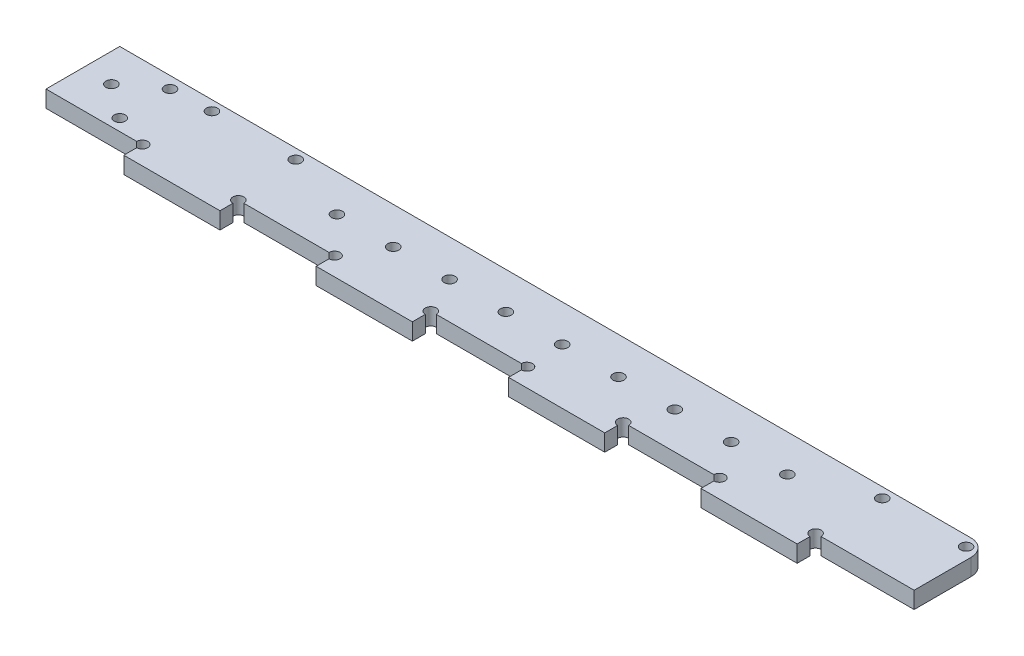
SolidWorks part; units mm, degrees
material "Acrylic (Medium-high impact)"
ref_plane "Front Plane" through (0, 0, 0) normal (0, 0, 1) x (1, 0, 0)
ref_plane "Top Plane" through (0, 0, 0) normal (0, 1, 0) x (1, 0, 0)
ref_plane "Right Plane" through (0, 0, 0) normal (1, 0, 0) x (0, 0, -1)
sketch "Sketch1" plane through (0, 0, 0) normal (0, 1, 0) x (1, 0, 0)
  line L0 (230.5, 19) -> (255.5, 19) construction
  line L1 (0, 0) -> (227, 0)
  line L2 (0, 0) -> (0, 22)
  line L3 (0, 22) -> (227, 22)
  line L5 (227, 22) -> (259, 22)
  line L6 (227, 22) -> (227, 0) construction
  line L7 (227, 0) -> (259, 0)
  line L8 (259, 22) -> (259, 0)
  line L9 (243, 19) -> (243, 13.1174) construction
  line L10 (27, 22) -> (27, 0) construction
  line L11 (59, 22) -> (59, 0) construction
  line L12 (27, 19) -> (59, 19) construction
  line L13 (43, 19) -> (43, 9.4741) construction
  line L14 (22, 22) -> (22, 0) construction
  line L15 (0, 11) -> (22, 11) construction
  line L16 (18.5, 22) -> (18.5, 0) construction
  line L17 (15, 0) -> (19, 0) construction
  circle A0 centre (230.5, 19) radius 1.65
  circle A1 centre (255.5, 19) radius 1.65
  circle A2 centre (30.5, 19) radius 1.65
  circle A3 centre (55.5, 19) radius 1.65
  circle A5 centre (8.5, 11) radius 1.65
  circle A6 centre (18.5, 18.5) radius 1.65
  circle A7 centre (18.5, 3.5) radius 1.65
  dimension "D3" = 3.3
  dimension "D1" = 22
  dimension "D2" = 32
  dimension "D4" = 25
  dimension "D5" = 19
  dimension "D6" = 25
  dimension "D7" = 32
  dimension "D8" = 200
  dimension "D9" = 22
  dimension "D10" = 5
  dimension "D11" = 8.5
  dimension "D12" = 3.5
  dimension "D13" = 3.5
  dimension "D14" = 3.5
extrude "Boss-Extrude1" add sketch "Sketch1" along normal blind 5
sketch "Sketch4" plane through (0, 5, 0) normal (0, 1, 0) x (1, 0, 0)
  line L0 (0, 0) -> (259, 0)
  line L1 (0, 0) -> (0, -5.5) construction
  line L2 (0, -5.5) -> (28.7, -5.5) construction
  line L3 (28.7, -5.5) -> (28.7, 0)
  line L4 (28.7, 0) -> (28.7, -5.5)
  line L5 (28.7, -5.5) -> (57.4, -5.5)
  line L6 (57.4, -5.5) -> (57.4, 0)
  line L7 (57.4, 0) -> (57.4, -5.5)
  line L8 (57.4, -5.5) -> (86.1, -5.5)
  line L9 (86.1, -5.5) -> (86.1, 0)
  line L10 (86.1, 0) -> (86.1, -5.5)
  line L11 (86.1, -5.5) -> (114.8, -5.5)
  line L12 (114.8, -5.5) -> (114.8, 0)
  line L13 (114.8, 0) -> (114.8, -5.5)
  line L14 (114.8, -5.5) -> (143.5, -5.5)
  line L15 (143.5, -5.5) -> (143.5, 0)
  line L16 (143.5, 0) -> (143.5, -5.5)
  line L17 (143.5, -5.5) -> (172.2, -5.5)
  line L18 (172.2, -5.5) -> (172.2, 0)
  line L19 (172.2, 0) -> (172.2, -5.5)
  line L20 (172.2, -5.5) -> (200.9, -5.5)
  line L21 (200.9, -5.5) -> (200.9, 0)
  line L22 (200.9, 0) -> (200.9, -5.5)
  line L23 (200.9, -5.5) -> (229.6, -5.5)
  line L24 (229.6, -5.5) -> (229.6, 0)
  line L25 (229.6, 0) -> (229.6, -5.5)
  line L26 (229.6, -5.5) -> (258.3, -5.5)
  line L27 (258.3, -5.5) -> (258.3, 0)
  dimension "D1" = 5.5
  dimension "D2" = 28.7
  dimension "D3" = 9
extrude "Boss-Extrude3" add sketch "Sketch4" against normal blind 5 contours L5 L6 L0 L3 | L11 L12 L0 L10 | L17 L18 L0 L16 | L23 L24 L0 L22
sketch "Sketch5" plane through (0, 5, 0) normal (0, 1, 0) x (1, 0, 0)
  circle A0 centre (28.7, 0) radius 1.65
  circle A1 centre (57.4, 0) radius 1.65
  circle A2 centre (86.1, 0) radius 1.65
  circle A3 centre (114.8, 0) radius 1.65
  circle A4 centre (143.5, 0) radius 1.65
  circle A5 centre (172.2, 0) radius 1.65
  circle A6 centre (200.9, 0) radius 1.65
  circle A7 centre (229.6, 0) radius 1.65
  dimension "D1" = 3.3
extrude "Cut-Extrude2" cut sketch "Sketch5" against normal through all
sketch "Sketch6" plane through (0, 5, 0) normal (0, 1, 0) x (1, 0, 0)
  line L0 (0, 11) -> (259, 11) construction
  line L1 (0, 22) -> (0, 0) construction
  line L2 (259, 0) -> (259, 22) construction
  line L3 (59, 22) -> (59, 3.8809) construction
  line L4 (259, 22) -> (0, 22) construction
  line L6 (55.5, 19) -> (55.5, 11) construction
  line L7 (230.5, 19) -> (230.5, 11) construction
  line L8 (227, 22) -> (227, 11) construction
  circle A0 centre (59, 11) radius 1.65 construction
  circle A1 centre (75.8, 11) radius 1.65
  circle A2 centre (92.6, 11) radius 1.65
  circle A3 centre (109.4, 11) radius 1.65
  circle A4 centre (126.2, 11) radius 1.65
  circle A5 centre (143, 11) radius 1.65
  circle A6 centre (159.8, 11) radius 1.65
  circle A7 centre (176.6, 11) radius 1.65
  circle A8 centre (193.4, 11) radius 1.65
  circle A9 centre (210.2, 11) radius 1.65
  dimension "D4" = 3.3
  dimension "D1" = 3.5
  dimension "D2" = 3.5
  dimension "D3" = 10
  dimension "D5" = 16.8
extrude "Cut-Extrude3" cut sketch "Sketch6" against normal through all
fillet "Fillet1" radius 5 1 edges at (259, 2.5, -22)
